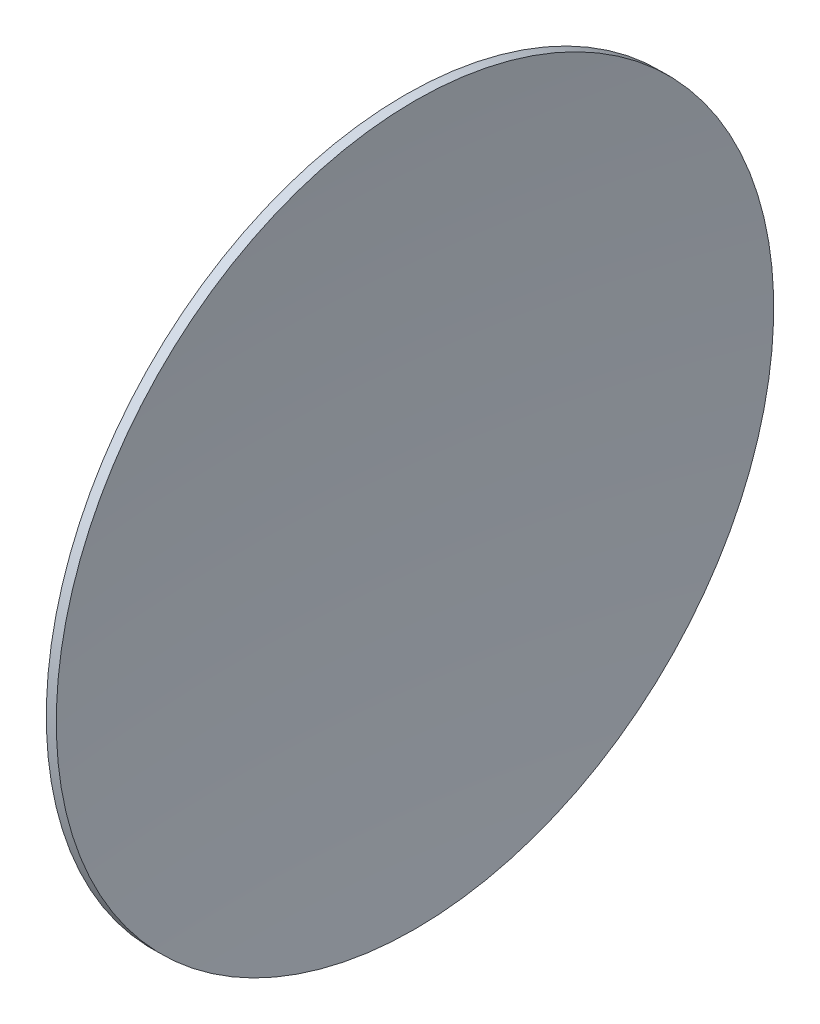
SolidWorks part; units mm, degrees
ref_plane "Front Plane" through (0, 0, 0) normal (0, 0, 1) x (1, 0, 0)
ref_plane "Top Plane" through (0, 0, 0) normal (0, 1, 0) x (1, 0, 0)
ref_plane "Right Plane" through (0, 0, 0) normal (1, 0, 0) x (0, 0, -1)
sketch "Sketch1" plane through (0, 0, 0) normal (0, 0, 1) x (1, 0, 0)
  line L0 (-9.4954, 5.1851) -> (-14.4954, 5.1851) construction
  line L1 (-9.4954, 25.2326) -> (-9.4954, -14.8624) construction
  line L2 (-14.4954, -12.8624) -> (-14.4954, 23.2326) construction
  line L3 (-14.4954, 5.1851) -> (-17.8931, 5.1851) construction
  line L4 (-17.8931, 5.1851) -> (-18.0322, 5.1851) construction
  line L5 (-16.9954, 23.2326) -> (-17.4979, 23.2326)
  line L6 (-18.0322, 5.1851) -> (-21.2258, 5.1851) construction
  line L7 (-17.8927, 5.1851) -> (-18.3927, 5.1851)
  arc A0 (-16.9954, 23.2326) -> (-17.8927, 5.1851) centre (164.0615, 5.1851) ccw
  arc A1 (-17.4979, 23.2326) -> (-18.3927, 5.1851) centre (164.0615, 5.1851) ccw
  arc A3 (-17.493, 23.2822) -> (-17.493, -12.912) centre (164.0615, 5.1851) ccw construction
  arc A4 (-16.9954, 23.2326) -> (-16.9954, -12.8624) centre (164.0615, 5.1851) ccw construction
  point P16 (-17.5022, 23.2326)
  dimension "D1" = 0.5
revolve "Revolve1" add sketch "Sketch1" angle 360 about L3
